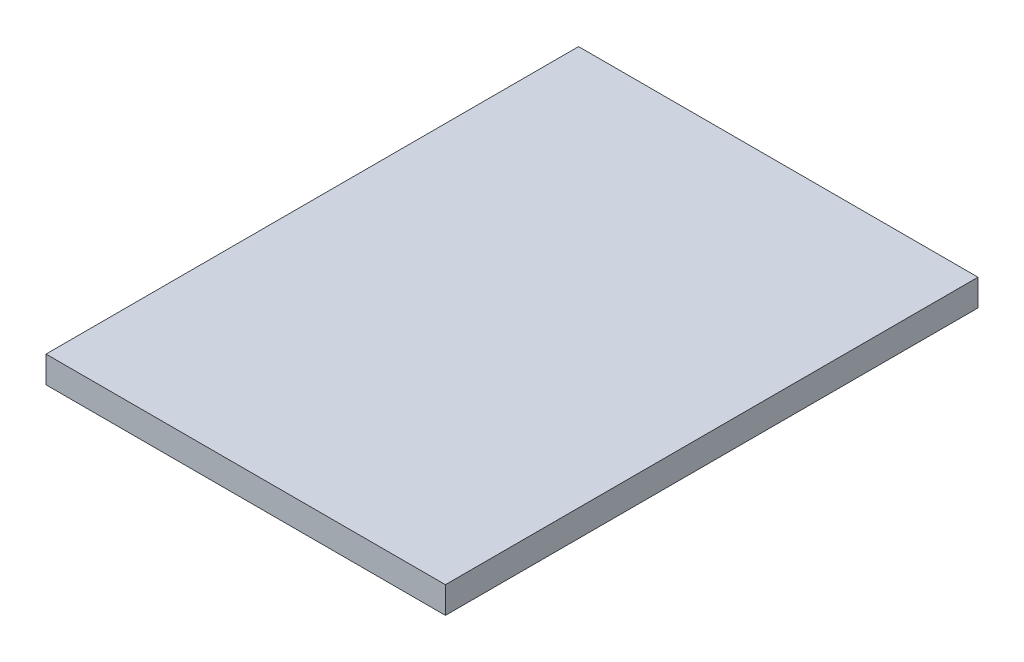
SolidWorks part; units mm, degrees
material "ПВХ Жесткий"
ref_plane "Спереди" through (0, 0, 0) normal (0, 0, 1) x (1, 0, 0)
ref_plane "Сверху" through (0, 0, 0) normal (0, 1, 0) x (1, 0, 0)
ref_plane "Справа" through (0, 0, 0) normal (1, 0, 0) x (0, 0, -1)
sketch "Эскиз1" plane through (0, 0, 0) normal (0, 1, 0) x (1, 0, 0)
  line L1 (0, 0) -> (150, 0)
  line L2 (0, 0) -> (0, 200)
  line L3 (0, 200) -> (150, 200)
  line L4 (150, 0) -> (150, 200)
  dimension "D1" = 200
  dimension "D2" = 150
extrude "Бобышка-Вытянуть1" add sketch "Эскиз1" along normal blind 10
